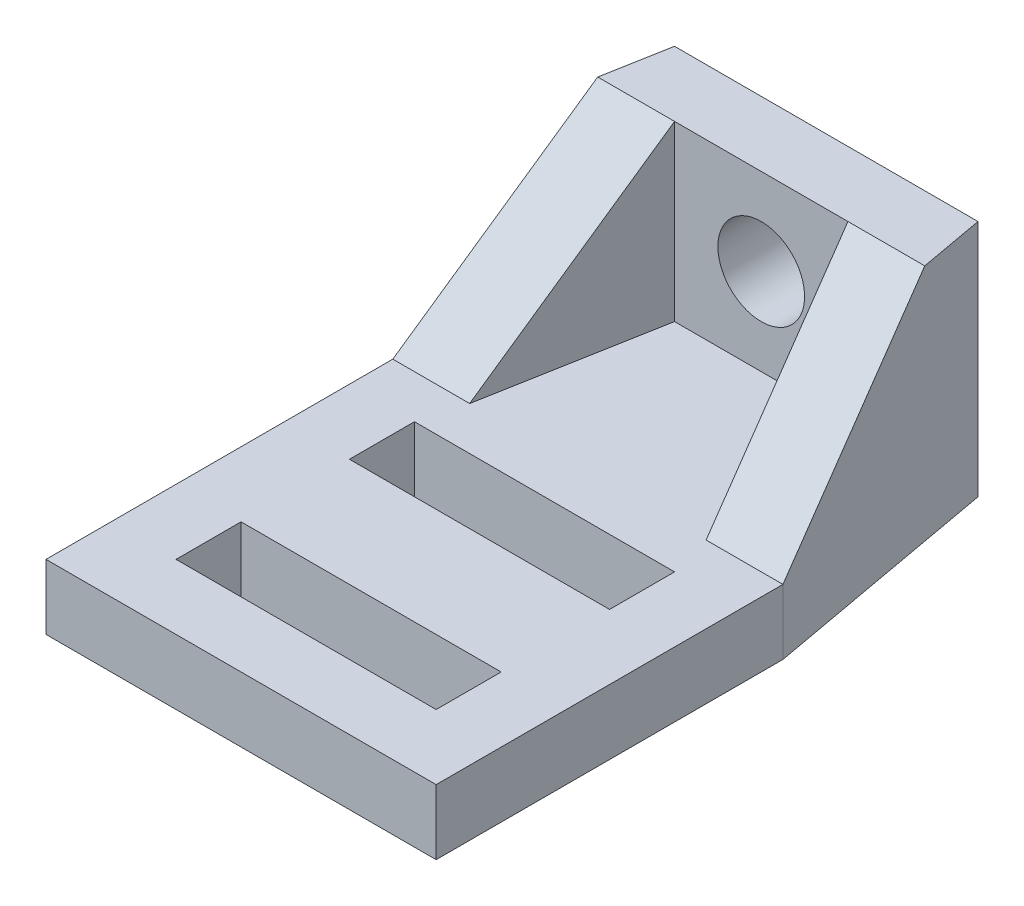
SolidWorks part; units mm, degrees
ref_plane "Ebene vorne" through (0, 0, 0) normal (0, 0, 1) x (1, 0, 0)
ref_plane "Ebene oben" through (0, 0, 0) normal (0, 1, 0) x (1, 0, 0)
ref_plane "Ebene rechts" through (0, 0, 0) normal (1, 0, 0) x (0, 0, -1)
sketch "Skizze1" plane through (0, 0, 0) normal (0, 1, 0) x (1, 0, 0)
  line L0 (0, -15.4281) -> (0, 20.7836) construction
  line L1 (9, -13.5) -> (-9, -13.5)
  line L2 (9, -13.5) -> (9, 2.5)
  line L3 (7, 13.5) -> (-7, 13.5)
  line L4 (-9, -13.5) -> (-9, 2.5)
  line L5 (7, 13.5) -> (9, 2.5)
  line L6 (-7, 13.5) -> (-9, 2.5)
  point P0 (0, 0)
  dimension "D3" = 14
  dimension "D5" = 11
  dimension "D6" = 11
extrude "Aufsatz-Linear austragen1" add sketch "Skizze1" along normal blind 3
sketch "Skizze2" plane through (0, 3, 0) normal (0, 1, 0) x (1, 0, 0)
  line L0 (-9, 2.5) -> (-7, 13.5)
  line L1 (-7, 13.5) -> (7, 13.5)
  line L2 (7, 13.5) -> (9, 2.5)
  line L3 (-4, 10.5) -> (4, 10.5)
  line L4 (-9, 2.5) -> (-5.4545, 2.5)
  line L5 (-4, 10.5) -> (-5.4545, 2.5)
  line L6 (4, 10.5) -> (5.4545, 2.5)
  line L7 (5.4545, 2.5) -> (9, 2.5)
  dimension "D1" = 3
  dimension "D2" = 3
  dimension "D3" = 3
extrude "Aufsatz-Linear austragen2" add sketch "Skizze2" along normal blind 8
sketch "Skizze3" plane through (-9, 0, 0) normal (-1, 0, 0) x (0, 0, 1)
  line L0 (-2.5, 3) -> (-10.5, 11)
  line L1 (-13.5, 11) -> (-2.5, 11) construction
  line L2 (-10.5, 11) -> (-10.5, 11.5485)
  line L3 (-10.5, 11.5485) -> (-1.6091, 11.5485)
  line L4 (-1.6091, 11.5485) -> (-1.6091, 3.6754)
  line L5 (-1.6091, 3.6754) -> (-2.5, 3)
  dimension "D1" = 45
extrude "Schnitt-Linear austragen1" cut sketch "Skizze3" against normal through all contours L4 L5 L0 L2 L3
hole_wizard "Ø4.0 (4) Durchmesser Bohrung1" positions "Skizze5" profile "Skizze6" hole size "Ø4.0" standard "DIN" end condition through all
sketch "Skizze5" plane through (0, 0, -13.5) normal (0, 0, -1) x (-1, 0, 0)
  line L0 (-7, 11) -> (7, 11) construction
  point P0 (0, 7)
  dimension "D1" = 4
sketch "Skizze6" plane through (0, 7, -13.5) normal (1, 0, 0) x (0, 1, 0)
  line L0 (0, 0) -> (0, 27)
  line L1 (0, 27) -> (2, 27)
  line L2 (2, 27) -> (2, 0)
  line L5 (2, 0) -> (0, 0)
  line L11 (0, -6.35) -> (0, 107.95) construction
  dimension "Bohrerdurchmesser" = 4
  dimension "Bohrungstiefe" = 27
sketch "Skizze7" plane through (0, 3, 0) normal (0, 1, 0) x (1, 0, 0)
  line L0 (-9, -13.5) -> (9, -13.5) construction
  line L1 (6, -10.5) -> (-6, -10.5)
  line L2 (6, -10.5) -> (6, -7.5)
  line L3 (6, -7.5) -> (-6, -7.5)
  line L4 (-6, -10.5) -> (-6, -7.5)
  line L5 (6, -10.5) -> (-6, -7.5) construction
  line L6 (6, -7.5) -> (-6, -10.5) construction
  line L7 (-9, 2.5) -> (-9, -13.5) construction
  line L8 (6, 0.5) -> (-6, 0.5)
  line L9 (6, 0.5) -> (6, -2.5)
  line L10 (6, -2.5) -> (-6, -2.5)
  line L11 (-6, 0.5) -> (-6, -2.5)
  line L12 (6, 0.5) -> (-6, -2.5) construction
  line L13 (6, -2.5) -> (-6, 0.5) construction
  point P0 (0, -9)
  point P7 (0, -1)
  dimension "D1" = 3
  dimension "D2" = 3
  dimension "D3" = 3
  dimension "D4" = 5
  dimension "D5" = 12
  dimension "D6" = 12
  dimension "D7" = 3
extrude "Schnitt-Linear austragen2" cut sketch "Skizze7" against normal through all
